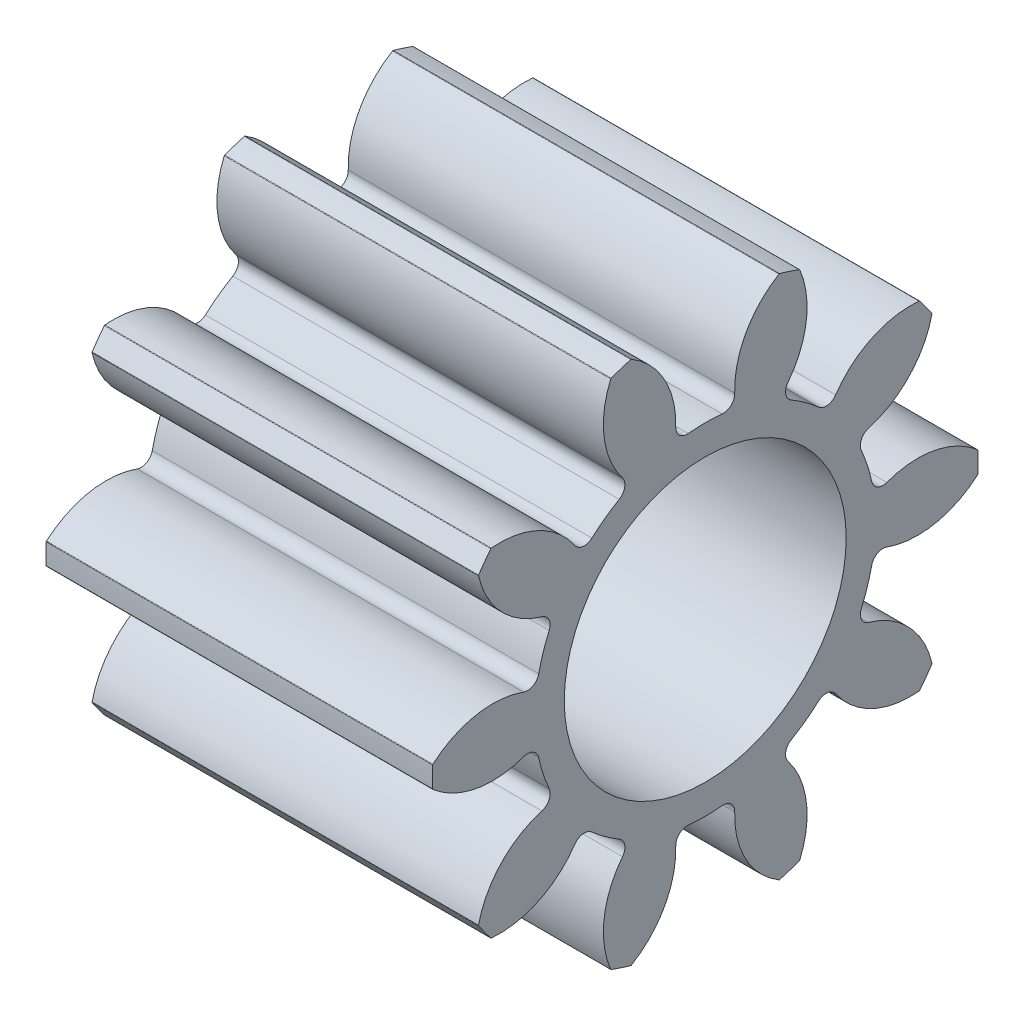
SolidWorks part; units mm, degrees
ref_plane "Plane1" through (0, 0, 0) normal (0, 0, 1) x (1, 0, 0)
ref_plane "Plane2" through (0, 0, 0) normal (0, 1, 0) x (1, 0, 0)
ref_plane "Plane3" through (0, 0, 0) normal (1, 0, 0) x (0, 0, -1)
sketch "HoldingSke" plane through (0, 0, 0) normal (0, 1, 0) x (1, 0, 0)
  line L0 (0, 0) -> (0.9848, -0.1736)
  line L1 (-15, 0) -> (100, 0) construction
  line L2 (0, 0) -> (-2.1039, 2.3779)
  line L3 (0, 0) -> (-11.863, 4.5341)
  line L4 (0, 0) -> (8.5048, 1.4996)
  line L5 (0, 0) -> (-46.8476, -17.4728)
  line L6 (0, 0) -> (-8.2896, -5.593)
  line L7 (-2.1039, 2.3779) -> (8.6586, 51.2059)
  line L8 (-76.2, 54.61) -> (-75.7, 54.61)
  line L9 (-67.7845, 28.3722) -> (-49.3413, 33.142)
  line L10 (-76.2, 71.12) -> (104.1128, 71.12)
  line L11 (0, 0) -> (-10, 0)
  line L12 (-76.2, 101.6) -> (-76.162, 101.6)
  line L13 (24.9733, 27.94) -> (52.9518, 28.4284)
  line L14 (24.9733, 27.94) -> (24.9743, 27.94)
  line L15 (24.9733, 27.94) -> (100.4006, 29.5858)
  line L16 (-63.627, -1) -> (-12.827, -1)
  circle A0 centre (0, 0) radius 1.5
  circle A1 centre (0, 0) radius 3.749
  circle A2 centre (0, 0) radius 37.5
  circle A3 centre (0, 0) radius 1.5
  dimension "MHD" = 7.498
  dimension "Hub_dia" = 75
  dimension "Bore" = 3
  dimension "MBD" = 3
  dimension "Num_teeth" = 10
  dimension "Pitch" = 1
  dimension "Overall_len" = 50
  dimension "Show_teeth" = 10
  dimension "Thickness" = 10
  dimension "OAL" = 50.0001
  dimension "T_dim" = 0.5
  dimension "Ap" = 14.5
  dimension "H" = 19.05
  dimension "Pitch_radius" = 180.3128
  dimension "Width" = 10
  dimension "Backlash" = 0.038
  dimension "Addendum_fac" = 1
  dimension "Dedendum_fac" = 1.25
  dimension "Clearance_fac" = 0.25
  dimension "Dedendum_add" = 0.001
  dimension "Module" = 1
sketch "BasProSke" plane through (0, 0, 0) normal (0, 1, 0) x (1, 0, 0)
  line L0 (-10, 0) -> (60, 0) construction
  line L1 (0, 0) -> (0, 6)
  line L2 (0, 0) -> (8.5, 0)
  line L3 (8.5, 0) -> (8.5, 6)
  line L4 (8.5, 6) -> (0, 6)
  dimension "Thickness" = 8.5
  dimension "Diameter" = 12
revolve "Base-Revolve" add sketch "BasProSke" angle 360 about L0
sketch "TooCutSke" plane through (0, 0, 0) normal (1, 0, 0) x (0, 0, -1)
  line L1 (0, 0) -> (0, 107) construction
  line L2 (0, 0) -> (-0.8485, 4.9275) construction
  line L3 (0, 0) -> (-3.0584, 9.4126) construction
  line L4 (-0.8485, 4.9275) -> (-1.5292, 4.7063) construction
  arc A0 (0.6809, 3.6866) -> (-0.6809, 3.6866) centre (0, 0) ccw
  arc A1 (1.66, 5.7922) -> (-1.66, 5.7922) centre (0, 0) ccw
  circle A2 centre (0, 0) radius 5 construction
  circle A3 centre (0, 0) radius 4.8407 construction
  arc A4 (-0.6809, 3.6866) -> (-1.66, 5.7922) centre (-2.6471, 4.0528) ccw
  arc A5 (1.66, 5.7922) -> (0.6809, 3.6866) centre (2.6471, 4.0528) ccw
  dimension "Root_dia" = 7.498
  dimension "Overcut_dia" = 12.0508
  dimension "Pitch_dia" = 10
  dimension "Base_dia" = 9.6815
  dimension "Flank_rad" = 2
  dimension "Half_ang" = 18
  dimension "Half_CT" = 0.7157
extrude "ToothCut" cut sketch "TooCutSke" along normal through all
fillet "Breaks" radius 0.02 2 edges at (4.25, 5.7745, -1.6294) (4.25, 5.7745, 1.6294)
fillet "RootFillets" radius 0.251 2 edges at (4.25, 3.6866, -0.6809) (4.25, 3.6866, 0.6809)
pattern_circular "TeethCuts" count 10 every 36 about axis through (-10, 0, 0) along (1, 0, 0) of "ToothCut", "RootFillets", "Breaks"
sketch "HubNeaOneSke" plane through (0, 0, 0) normal (-1, 0, 0) x (0, 0, 1)
  circle A0 centre (0, 0) radius 3.749
  dimension "Diameter" = 7.498
extrude "HubNearOne" [suppressed] add sketch "HubNeaOneSke" along normal blind 41.5001
sketch "HubNeaBotSke" plane through (0, 0, 0) normal (-1, 0, 0) x (0, 0, 1)
  circle A0 centre (0, 0) radius 3.749
  dimension "Diameter" = 7.498
extrude "HubNearBoth" [suppressed] add sketch "HubNeaBotSke" along normal blind 20.75
ref_plane "FarPln" through (8.5, 0, 0) normal (1, 0, 0) x (0, 0, -1)
sketch "HubFarSke" plane through (8.5, 0, 0) normal (1, 0, 0) x (0, 0, -1)
  circle A0 centre (0, 0) radius 3.749
  dimension "Diameter" = 7.498
extrude "HubFar" [suppressed] add sketch "HubFarSke" along normal blind 20.75
sketch "BorSke" plane through (0, 0, 0) normal (1, 0, 0) x (0, 0, -1)
  circle A0 centre (0, 0) radius 1.8
  dimension "Diameter" = 3.6
extrude "Bore" cut sketch "BorSke" along normal mid plane 100.0001
sketch "KeySke" plane through (0, 0, 0) normal (1, 0, 0) x (0, 0, -1)
  line L0 (-0.6, 0) -> (-0.6, 2)
  line L1 (-0.6, 2) -> (0.6, 2)
  line L2 (0.6, 2) -> (0.6, 0)
  line L3 (0, 0) -> (0, 34) construction
  line L4 (-0.6, 0) -> (0.6, 0)
  dimension "Offset" = 2
  dimension "Width" = 1.2
extrude "Keyway" [suppressed] cut sketch "KeySke" along normal mid plane 100.0001
pattern_circular "Keyway2" [suppressed] count 2 every 90 about axis through (-10, 0, 0) along (1, 0, 0)
sketch "Sketch3" plane through (0, 0, 0) normal (-1, 0, 0) x (0, 0, 1)
  circle A0 centre (0, 0) radius 2.5
  circle A1 centre (0, 0) radius 1.8 construction
  circle A2 centre (0, 0) radius 1.8
  dimension "D1" = 5
extrude "Boss-Extrude1" add sketch "Sketch3" along normal blind 1
sketch "Sketch4" plane through (8.5, 0, 0) normal (1, 0, 0) x (0, 0, -1)
  circle A0 centre (0, 0) radius 3.1
  dimension "D1" = 6.2
extrude "Cut-Extrude2" cut sketch "Sketch4" against normal blind 5
chamfer "Chamfer2" distance 0.5 angle 45 1 edges at (-1, 0, 2.5)
equation "' \"Module@HoldingSke\" = 6.35"
equation "' \"Num_teeth@HoldingSke\" = 12"
equation "' \"Ap@HoldingSke\" =  20"
equation "' \"Ap@HoldingSke\" = 20"
equation "' \"Width@HoldingSke\" = 0.5 * 25.4"
equation "' \"Hub_dia@HoldingSke\"= 1 * 25.4"
equation "' \"Hub_dia@HoldingSke\" = 1 * 25.4"
equation "' \"Overall_len@HoldingSke\" = 1.0 * 25.4"
equation "' \"Bore@HoldingSke\" = 0.75 * 25.4"
equation "' \"T_dim@HoldingSke\" = 0.1 * 25.4"
equation "' \"Width@KeySke\" = 0.25 * 25.4"
equation "' \"Show_teeth@HoldingSke\" = 13"
equation "' \"Backlash@HoldingSke\" = 0.009 * 25.4"
equation "' \"Addendum_fac@HoldingSke\" = 1.0"
equation "' \"Dedendum_fac@HoldingSke\" = 1.25"
equation "' \"Dedendum_add@HoldingSke\" = 0.00005 * 25.4"
equation "' \"Clearance_fac@HoldingSke\" = 0.25"
equation "\"Pitch@HoldingSke\" = 1 / \"Module@HoldingSke\""
equation "\"Overcut_dia@TooCutSke\" = (\"Num_teeth@HoldingSke\" + 2 * \"Addendum_fac@HoldingSke\") / \"Pitch@HoldingSke\" + 0.002 * 25.4"
equation "\"Pitch_dia@TooCutSke\" = \"Num_teeth@HoldingSke\" / \"Pitch@HoldingSke\""
equation "\"Base_dia@TooCutSke\" = \"Num_teeth@HoldingSke\" / \"Pitch@HoldingSke\" * cos((\"Ap@HoldingSke\"  * 3.14159265 / 180))"
equation "\"Root_dia@TooCutSke\" = (\"Num_teeth@HoldingSke\" + 2) / \"Pitch@HoldingSke\" - 2 * (\"Addendum_fac@HoldingSke\" + \"Dedendum_fac@HoldingSke\") / \"Pitch@HoldingSke\" - \"Dedendum_add@HoldingSke\" * 2"
equation "\"Half_ang@TooCutSke\" = 180 / \"Num_teeth@HoldingSke\""
equation "\"Half_CT@TooCutSke\" = \"Num_teeth@HoldingSke\" / \"Pitch@HoldingSke\" * sin((3.14159265 / 2 / \"Num_teeth@HoldingSke\")) / 2 - 7 * \"Backlash@HoldingSke\" / 4"
equation "\"Flank_rad@TooCutSke\" = \"Num_teeth@HoldingSke\" / \"Pitch@HoldingSke\" / 5"
equation "\"Radius@RootFillets\" = \"Clearance_fac@HoldingSke\" / \"Pitch@HoldingSke\" + \"Dedendum_add@HoldingSke\""
equation "\"Break_rad@Breaks\" = 0.02 / \"Pitch@HoldingSke\""
equation "\"Thickness@HoldingSke\" = \"Width@HoldingSke\""
equation "\"OAL@HoldingSke\" = \"Thickness@HoldingSke\""
equation "\"MHD@HoldingSke\" = (\"Num_teeth@HoldingSke\" + 2) / \"Pitch@HoldingSke\" - 2 * (\"Addendum_fac@HoldingSke\" + \"Dedendum_fac@HoldingSke\")  / \"Pitch@HoldingSke\" - \"Dedendum_add@HoldingSke\" * 2"
equation "\"MBD@HoldingSke\" = (\"Num_teeth@HoldingSke\" + 2) / \"Pitch@HoldingSke\" - 2 * (\"Addendum_fac@HoldingSke\" + \"Dedendum_fac@HoldingSke\")  / \"Pitch@HoldingSke\" - \"Dedendum_add@HoldingSke\" * 2 - 0.002 * 25.4"
equation "\"MHD@HoldingSke\" = ((sgn( \"MHD@HoldingSke\" - \"Hub_dia@HoldingSke\" )-1)*( \"MHD@HoldingSke\" - \"Hub_dia@HoldingSke\" ))/-2+ \"Hub_dia@HoldingSke\""
equation "\"MBD@HoldingSke\" = ((sgn( \"MBD@HoldingSke\" - \"Bore@HoldingSke\" )-1)*( \"MBD@HoldingSke\" - \"Bore@HoldingSke\" ))/-2+ \"Bore@HoldingSke\""
equation "\"OAL@HoldingSke\" = ((sgn( \"OAL@HoldingSke\" - \"Overall_len@HoldingSke\" )+1)*( \"OAL@HoldingSke\" - \"Overall_len@HoldingSke\" ))/2 + \"Overall_len@HoldingSke\" + 0.000002 * 25.4"
equation "\"Num_teeth@TeethCuts\" = int( \"Show_teeth@HoldingSke\" ) + 1"
equation "\"Num_teeth@TeethCuts\" = ((sgn( \"Num_teeth@TeethCuts\" - \"Num_teeth@HoldingSke\" )-1)*( \"Num_teeth@TeethCuts\" - \"Num_teeth@HoldingSke\" ))/-2+ \"Num_teeth@HoldingSke\""
equation "\"Num_teeth@TeethCuts\" = ((sgn( \"Num_teeth@TeethCuts\" - 2.0)+1)*( \"Num_teeth@TeethCuts\" - 2.0))/2 +2.0"
equation "\"Angle@TeethCuts\" = 360.0 / \"Num_teeth@HoldingSke\""
equation "\"Diameter@BasProSke\" = (\"Num_teeth@HoldingSke\" + 2 * \"Addendum_fac@HoldingSke\") / \"Pitch@HoldingSke\""
equation "' \"Fillet_rad@BasProSke\" =  \"Thickness@HoldingSke\" * 0.05"
equation "' \"Fillet_rad@BasProSke\" = \"Thickness@HoldingSke\" * 0.05"
equation "\"MHD@HoldingSke\" = ((sgn( \"MHD@HoldingSke\" - \"Root_dia@TooCutSke\" )-1)*( \"MHD@HoldingSke\" - \"Root_dia@TooCutSke\" ))/-2+ \"Root_dia@TooCutSke\""
equation "\"Diameter@HubNeaOneSke\" = \"MHD@HoldingSke\""
equation "\"Length@HubNearOne\" = \"OAL@HoldingSke\" - \"Thickness@BasProSke\""
equation "\"Diameter@HubNeaBotSke\" = \"MHD@HoldingSke\""
equation "\"Length@HubNearBoth\" = ( \"OAL@HoldingSke\" - \"Thickness@BasProSke\" ) / 2.0"
equation "\"Thickness@FarPln\" = \"Thickness@BasProSke\""
equation "\"Diameter@HubFarSke\" = \"MHD@HoldingSke\""
equation "\"Length@HubFar\" = ( \"OAL@HoldingSke\" - \"Thickness@BasProSke\" ) / 2.0"
equation "\"D1@Bore\" = \"OAL@HoldingSke\" * 2.0"
equation "\"D1@Keyway\" = \"OAL@HoldingSke\" * 2.0"
equation "\"Offset@KeySke\" = \"T_dim@HoldingSke\" + \"MBD@HoldingSke\" / 2.0"
